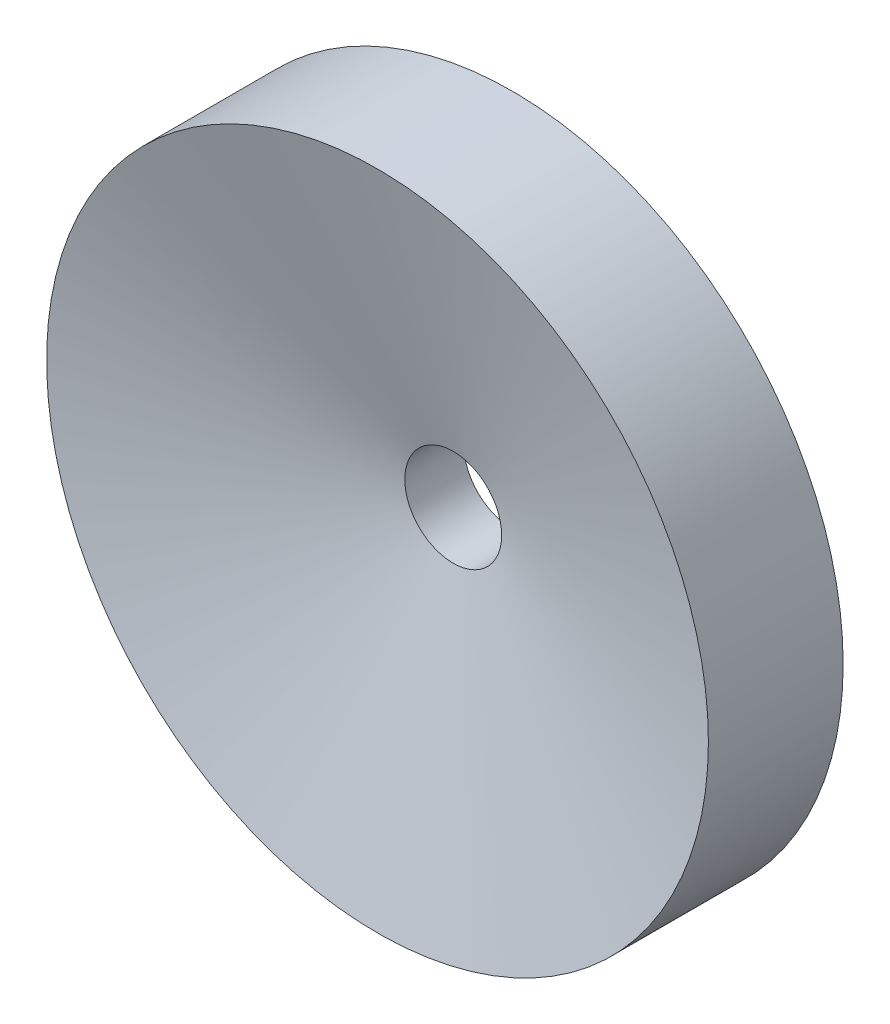
SolidWorks part; units mm, degrees
ref_plane "前视基准面" through (0, 0, 0) normal (0, 0, 1) x (1, 0, 0)
ref_plane "上视基准面" through (0, 0, 0) normal (0, 1, 0) x (1, 0, 0)
ref_plane "右视基准面" through (0, 0, 0) normal (1, 0, 0) x (0, 0, -1)
sketch "草图1" plane through (0, 0, 0) normal (0, 0, 1) x (1, 0, 0)
  circle A0 centre (0, 0) radius 14
  dimension "D1" = 28
extrude "凸台-拉伸1" add sketch "草图1" along normal blind 2.5
sketch "草图2" plane through (0, 0, 0) normal (0, 0, -1) x (-1, 0, 0)
  line L0 (-22.74, 0) -> (25.0557, 0) construction
  line L1 (0, 36.0144) -> (0, -30.4233) construction
  circle A0 centre (-9.5, 0) radius 1.45
  circle A1 centre (0, 8) radius 1.45
  circle A2 centre (0, -8) radius 1.45
  circle A3 centre (9.5, 0) radius 1.45
  point P13 (0, 0)
  point P14 (0, -20.561)
  point P15 (0, -30.4233)
  dimension "D1" = 2.9
  dimension "D2" = 2.9
  dimension "D3" = 19
  dimension "D4" = 16
extrude "凸台-拉伸2" add sketch "草图2" along normal blind 1.5
sketch "草图3" plane through (0, 0, 2.5) normal (0, 0, 1) x (1, 0, 0)
  circle A0 centre (0, 0) radius 2.05
  dimension "D1" = 4.1
extrude "切除-拉伸1" cut sketch "草图3" against normal through all
sketch "草图4" plane through (0, 0, 0) normal (1, 0, 0) x (0, 0, -1)
  line L0 (-14.6046, 0) -> (15.6015, 0) construction
  line L1 (-2.5, 2.05) -> (-5.702, 14)
  line L2 (-2.5, 14) -> (-2.5, -14) construction
  line L3 (-5.702, 14) -> (-2.5, 14)
  line L4 (-2.5, 14) -> (-2.5, 2.05)
  line L5 (0, 14) -> (-2.5, 14) construction
  line L6 (-2.5, 2.05) -> (-2.5, -2.05) construction
  point P8 (0, 0)
  point P10 (-4.8252, 14.218)
  dimension "D1" = 2.05
  dimension "D2" = 15
revolve "旋转1" add sketch "草图4" angle 360 about L0
